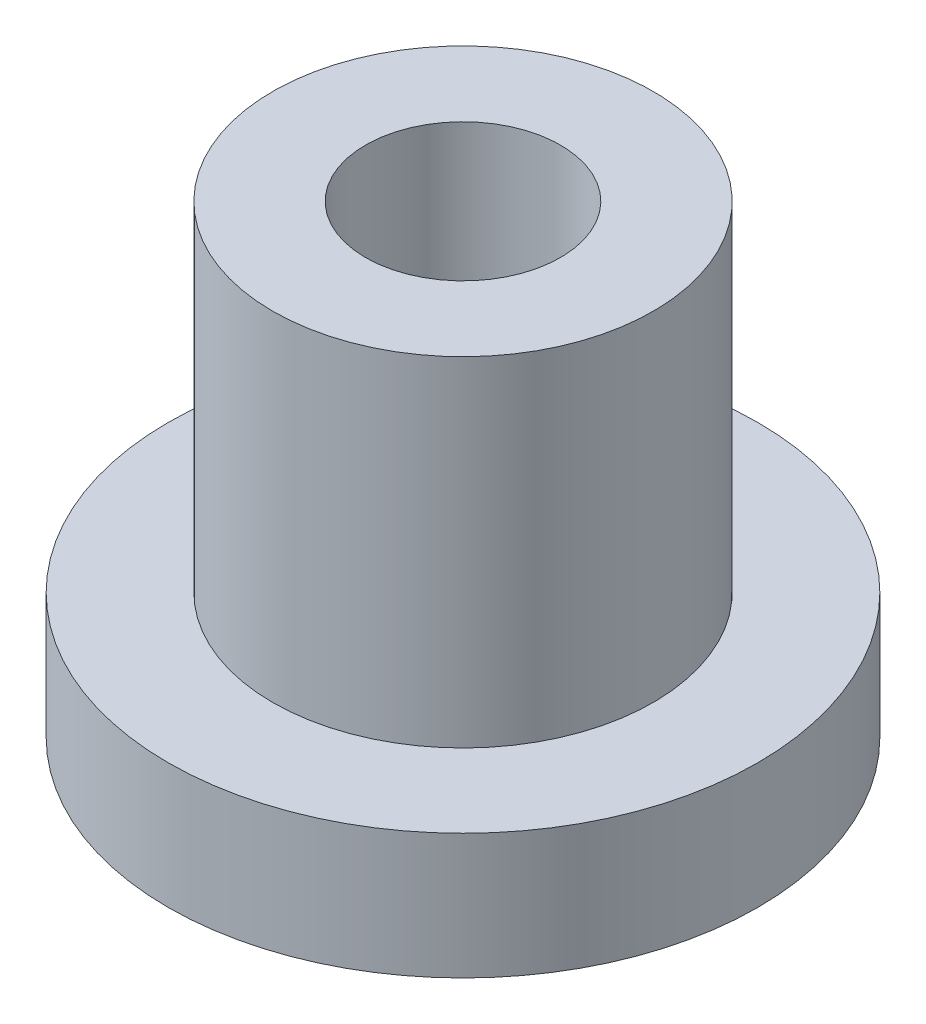
SolidWorks part; units mm, degrees
ref_plane "Front Plane" through (0, 0, 0) normal (0, 0, 1) x (1, 0, 0)
ref_plane "Top Plane" through (0, 0, 0) normal (0, 1, 0) x (1, 0, 0)
ref_plane "Right Plane" through (0, 0, 0) normal (1, 0, 0) x (0, 0, -1)
sketch "Sketch1" plane through (0, 0, 0) normal (0, 1, 0) x (1, 0, 0)
  circle A0 centre (0, 0) radius 6.35
  dimension "D1" = 12.7
extrude "base_body" add sketch "Sketch1" along normal blind 10
sketch "Sketch2" plane through (0, 10, 0) normal (0, 1, 0) x (1, 0, 0)
  circle A0 centre (0, 0) radius 2.1
  dimension "D1" = 4.2
extrude "shaft_bearing_cut" cut sketch "Sketch2" against normal through all
sketch "Sketch3" plane through (0, 10, 0) normal (0, 1, 0) x (1, 0, 0)
  circle A0 centre (0, 0) radius 4.1
  dimension "D1" = 8.2
extrude "lathe_cut" cut sketch "Sketch3" against normal blind 7.3 flip side to cut
